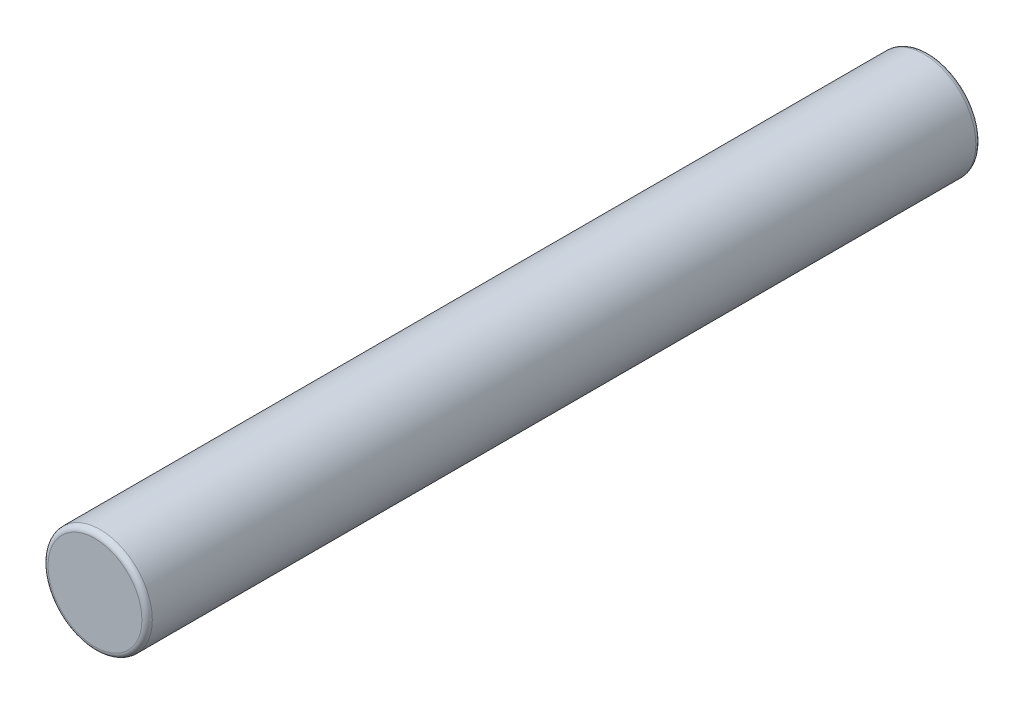
SolidWorks part; units mm, degrees
ref_plane "Front Plane" through (0, 0, 0) normal (0, 0, 1) x (1, 0, 0)
ref_plane "Top Plane" through (0, 0, 0) normal (0, 1, 0) x (1, 0, 0)
ref_plane "Right Plane" through (0, 0, 0) normal (1, 0, 0) x (0, 0, -1)
sketch "Sketch2" plane through (0, 0, 0) normal (0, 0, 1) x (1, 0, 0)
  circle A0 centre (-44.489, 13.7312) radius 1
extrude "Boss-Extrude2" add sketch "Sketch2" along normal blind 16
fillet "Fillet1" radius 0.1 2 edges at (-43.489, 13.7312, 0) (-43.489, 13.7312, 16)
